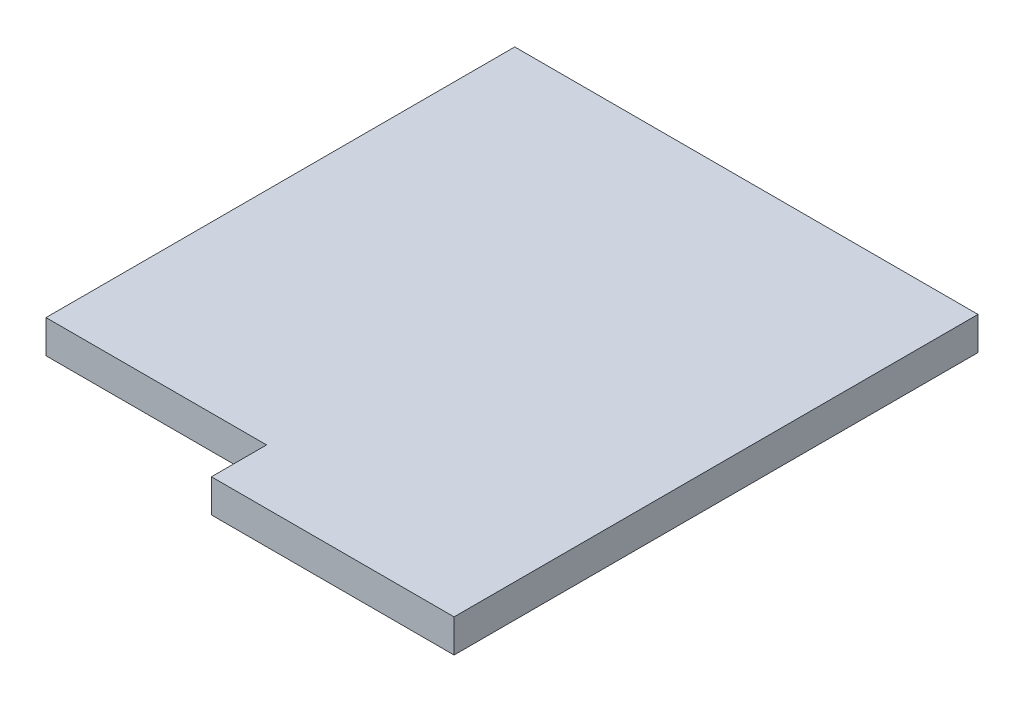
SolidWorks part; units mm, degrees
ref_plane "Front Plane" through (0, 0, 0) normal (0, 0, 1) x (1, 0, 0)
ref_plane "Top Plane" through (0, 0, 0) normal (0, 1, 0) x (1, 0, 0)
ref_plane "Right Plane" through (0, 0, 0) normal (1, 0, 0) x (0, 0, -1)
sketch "Sketch1" plane through (0, 0, 0) normal (0, 1, 0) x (1, 0, 0)
  line L1 (-21, -23.75) -> (21, -23.75)
  line L2 (-21, -23.75) -> (-21, 23.75)
  line L3 (-21, 23.75) -> (21, 23.75)
  line L4 (21, -23.75) -> (21, 23.75)
  line L5 (-21, -23.75) -> (21, 23.75) construction
  line L6 (-21, 23.75) -> (21, -23.75) construction
  point P0 (0, 0)
  dimension "D1" = 42
  dimension "D2" = 47.5
extrude "Boss-Extrude1" add sketch "Sketch1" along normal blind 3
sketch "Sketch2" plane through (0, 0, 0) normal (0, 1, 0) x (1, 0, 0)
  line L0 (-5.8041, 23.75) -> (34.6986, 23.75) construction
  line L2 (21, 13.7848) -> (21, 27.0334) construction
  line L4 (3.7853, -23.75) -> (28.579, -23.75) construction
  line L6 (-21, -7.3498) -> (-21, -26.8441) construction
  line L8 (-1, 31.6336) -> (-1, -33.1267) construction
  line L9 (-53.2018, -18.75) -> (53.452, -18.75) construction
  line L11 (-21, -23.75) -> (-1, -23.75)
  line L12 (-21, -23.75) -> (-21, -18.75)
  line L13 (-21, -18.75) -> (-1, -18.75)
  line L14 (-1, -23.75) -> (-1, -18.75)
  point P6 (-21, -18.75)
  point P10 (-1, -18.75)
  point P11 (-1, -23.75)
  point P15 (-21, -23.75)
  dimension "D1" = 5
  dimension "D2" = 20
extrude "Cut-Extrude1" cut sketch "Sketch2" along normal blind 5
